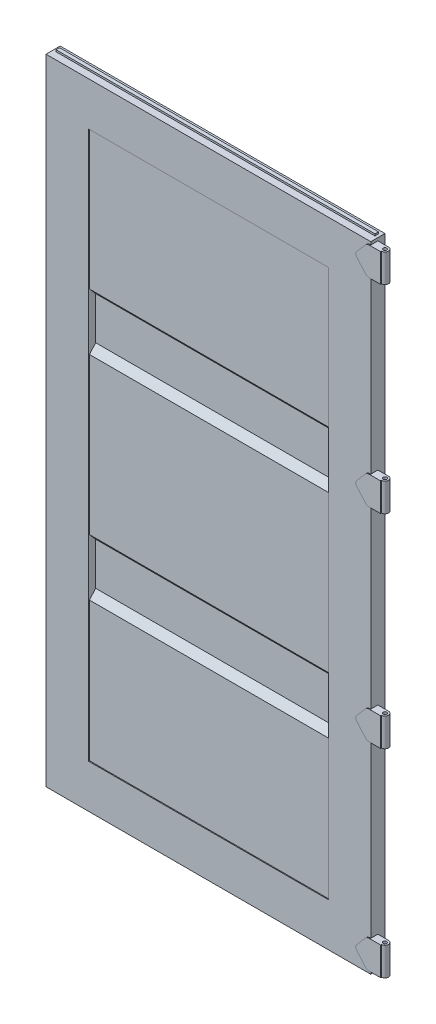
SolidWorks part; units mm, degrees
material "AISI 304"
ref_plane "Front Plane" through (0, 0, 0) normal (0, 0, 1) x (1, 0, 0)
ref_plane "Top Plane" through (0, 0, 0) normal (0, 1, 0) x (1, 0, 0)
ref_plane "Right Plane" through (0, 0, 0) normal (1, 0, 0) x (0, 0, -1)
sketch "Sketch2" plane through (0, 0, 0) normal (0, 1, 0) x (1, 0, 0)
  line L1 (-581.8187, 25.4) -> (-429.4187, 25.4)
  line L2 (-581.8187, 25.4) -> (-581.8187, -25.4)
  line L3 (-581.8187, -25.4) -> (-429.4187, -25.4)
  line L4 (-429.4187, 25.4) -> (-429.4187, -25.4)
  line L5 (-581.8187, 25.4) -> (-429.4187, -25.4) construction
  line L6 (-581.8187, -25.4) -> (-429.4187, 25.4) construction
  line L7 (581.8187, 25.4) -> (429.4187, 25.4)
  line L8 (581.8187, 25.4) -> (581.8187, -25.4)
  line L9 (581.8187, -25.4) -> (429.4187, -25.4)
  line L10 (429.4187, 25.4) -> (429.4187, -25.4)
  line L11 (581.8187, 25.4) -> (429.4187, -25.4) construction
  line L12 (581.8187, -25.4) -> (429.4187, 25.4) construction
  line L16 (578.6437, 22.225) -> (578.6437, -22.225)
  line L17 (578.6437, -22.225) -> (432.5937, -22.225)
  line L18 (432.5937, 22.225) -> (432.5937, -22.225)
  line L19 (578.6437, 22.225) -> (432.5937, 22.225)
  line L20 (-578.6437, 22.225) -> (-578.6437, -22.225)
  line L21 (-578.6437, -22.225) -> (-432.5937, -22.225)
  line L22 (-432.5937, 22.225) -> (-432.5937, -22.225)
  line L23 (-578.6437, 22.225) -> (-432.5937, 22.225)
  point P0 (-505.6187, 0)
  point P5 (505.6187, 0)
  point P10 (0, 0)
  point P11 (0, 0)
  point P12 (0, 0)
  point P13 (0, 0)
  dimension "D1" = 1163.6375
  dimension "D2" = 50.8
  dimension "D3" = 152.4
  dimension "D4" = 152.4
  dimension "D5" = 581.8187
  dimension "D6" = 3.175
  dimension "D7" = 3.175
extrude "Boss-Extrude1" add sketch "Sketch2" along normal mid plane 2266.95
sketch "Sketch3" plane through (429.4187, 0, 0) normal (-1, 0, 0) x (0, 0, 1)
  line L0 (19.05, 987.425) -> (0, 987.425)
  line L1 (0, 987.425) -> (0, 981.075)
  line L2 (0, 981.075) -> (25.4, 981.075)
  line L3 (25.4, 1133.475) -> (25.4, -1133.475) construction
  line L4 (25.4, 981.075) -> (25.4, 1133.475)
  line L5 (25.4, 1133.475) -> (-25.4, 1133.475)
  line L6 (-25.4, 1133.475) -> (-25.4, 1127.125)
  line L7 (-25.4, 1133.475) -> (-25.4, -1133.475) construction
  line L8 (-25.4, 1127.125) -> (19.05, 1127.125)
  line L9 (19.05, 1127.125) -> (19.05, 987.425)
  line L10 (-25.4, -1133.475) -> (25.4, -1133.475)
  line L11 (25.4, -1133.475) -> (25.4, -981.075)
  line L12 (25.4, -981.075) -> (0, -981.075)
  line L13 (0, -981.075) -> (0, -987.425)
  line L14 (0, -987.425) -> (19.05, -987.425)
  line L15 (19.05, -987.425) -> (19.05, -1127.125)
  line L16 (19.05, -1127.125) -> (-25.4, -1127.125)
  line L17 (-25.4, -1127.125) -> (-25.4, -1133.475)
  dimension "D1" = 6.35
  dimension "D2" = 6.35
  dimension "D3" = 6.35
  dimension "D4" = 152.4
  dimension "D5" = 25.4
  dimension "D6" = 6.35
  dimension "D7" = 6.35
  dimension "D8" = 6.35
  dimension "D9" = 25.4
  dimension "D10" = 152.4
extrude "Boss-Extrude4" add sketch "Sketch3" along normal up to surface (858.8375 mm away) up to face at (-429.4187, 0, 0)
sketch "Sketch5" plane through (-581.8187, 0, 0) normal (-1, 0, 0) x (0, 0, 1)
  line L0 (-25.4, -1133.475) -> (25.4, -1133.475) construction
  line L1 (-25.4, -1130.3) -> (25.4, -1130.3)
  line L2 (-25.4, -1130.3) -> (-25.4, -1136.65)
  line L3 (-25.4, -1136.65) -> (25.4, -1136.65)
  line L4 (25.4, -1130.3) -> (25.4, -1136.65)
  line L5 (-25.4, -1130.3) -> (25.4, -1136.65) construction
  line L6 (-25.4, -1136.65) -> (25.4, -1130.3) construction
  line L7 (-25.4, 1136.65) -> (25.4, 1136.65)
  line L8 (-25.4, 1136.65) -> (-25.4, 1130.3)
  line L9 (-25.4, 1130.3) -> (25.4, 1130.3)
  line L10 (25.4, 1136.65) -> (25.4, 1130.3)
  line L11 (-25.4, 1136.65) -> (25.4, 1130.3) construction
  line L12 (-25.4, 1130.3) -> (25.4, 1136.65) construction
  line L13 (25.4, 1133.475) -> (25.4, -1133.475) construction
  line L14 (-25.4, 1133.475) -> (25.4, 1133.475) construction
  point P0 (0, -1133.475)
  point P5 (0, 1133.475)
  point P12 (0, -1133.475)
  point P17 (0, 1133.475)
  dimension "D1" = 6.35
  dimension "D2" = 6.35
extrude "Boss-Extrude5" add sketch "Sketch5" against normal up to surface (1163.6375 mm away) up to face at (581.8187, 0, 0)
sketch "Sketch6" plane through (-429.4187, 0, 0) normal (1, 0, 0) x (0, 0, -1)
  line L0 (-15.875, -981.075) -> (-15.875, -482.6)
  line L1 (-25.4, -981.075) -> (0, -981.075) construction
  line L2 (-15.875, -482.6) -> (6.35, -457.2)
  line L3 (6.35, -457.2) -> (6.35, -304.8)
  line L4 (6.35, -304.8) -> (-15.875, -279.4)
  line L5 (-15.875, -279.4) -> (-15.875, 279.4)
  line L6 (-15.875, 279.4) -> (6.35, 304.8)
  line L7 (6.35, 304.8) -> (6.35, 457.2)
  line L8 (6.35, 457.2) -> (-15.875, 482.6)
  line L9 (-15.875, 482.6) -> (-15.875, 981.075)
  line L10 (0, 981.075) -> (-25.4, 981.075) construction
  line L11 (-15.875, 981.075) -> (-22.225, 981.075)
  line L12 (-22.225, 981.075) -> (-22.225, 482.6)
  line L13 (-22.225, 482.6) -> (0, 457.2)
  line L14 (0, 457.2) -> (0, 304.8)
  line L15 (0, 304.8) -> (-22.225, 279.4)
  line L16 (-22.225, 279.4) -> (-22.225, -279.4)
  line L17 (-22.225, -279.4) -> (0, -304.8)
  line L18 (0, -304.8) -> (0, -457.2)
  line L19 (0, -457.2) -> (-22.225, -482.6)
  line L20 (-22.225, -482.6) -> (-22.225, -981.075)
  line L21 (-22.225, -981.075) -> (-15.875, -981.075)
  line L22 (-25.4, 981.075) -> (-25.4, -981.075) construction
  point P14 (0, 0)
  point P28 (0, 0)
  point P29 (0, 0)
  point P30 (0, 0)
  point P31 (0, 0)
  point P32 (0, 247.428)
  point P33 (0, 399.828)
  point P34 (0, 0)
  point P35 (0, 0)
  point P36 (0, 0)
  point P37 (6.35, -492.0279)
  point P38 (0, 0)
  point P39 (6.35, -341.7856)
  point P40 (6.35, 191.7726)
  point P41 (-15.875, 0)
  point P42 (0, -381)
  point P43 (0, 381)
  dimension "D1" = 6.35
  dimension "D2" = 3.175
  dimension "D3" = 152.4
  dimension "D4" = 25.4
  dimension "D5" = 25.4
  dimension "D6" = 152.4
  dimension "D7" = 25.4
  dimension "D8" = 25.4
  dimension "D9" = 762
extrude "Boss-Extrude6" add sketch "Sketch6" along normal up to surface (858.8375 mm away) up to face at (429.4187, 0, 6.35)
sketch "Sketch1" plane through (0, 0, 0) normal (0, 0, 1) x (1, 0, 0)
  line L1 (-571.5, 1143) -> (571.5, 1143)
  line L2 (-571.5, 1143) -> (-571.5, -1143)
  line L3 (-571.5, -1143) -> (571.5, -1143)
  line L4 (571.5, 1143) -> (571.5, -1143)
  line L5 (-571.5, 1143) -> (571.5, -1143) construction
  line L6 (-571.5, -1143) -> (571.5, 1143) construction
  line L7 (571.5, 1123.95) -> (-571.5, 1123.95)
  line L8 (571.5, 1123.95) -> (571.5, -1123.95)
  line L9 (571.5, -1123.95) -> (-571.5, -1123.95)
  line L10 (-571.5, 1123.95) -> (-571.5, -1123.95)
  line L11 (571.5, 1123.95) -> (-571.5, -1123.95) construction
  line L12 (571.5, -1123.95) -> (-571.5, 1123.95) construction
  point P0 (0, 0)
  point P6 (0, 0)
  dimension "D1" = 1143
  dimension "D2" = 2286
  dimension "D3" = 19.05
sketch "Sketch7" plane through (0, 0, 25.4) normal (0, 0, 1) x (1, 0, 0)
  line L0 (571.5, 1143) -> (571.5, -1143) construction
  line L1 (533.4, 1126.49) -> (635, 1126.49)
  line L2 (533.4, 1126.49) -> (533.4, 1024.89)
  line L3 (533.4, 1024.89) -> (635, 1024.89)
  line L4 (635, 1126.49) -> (635, 1024.89)
  line L5 (533.4, 1126.49) -> (635, 1024.89) construction
  line L6 (533.4, 1024.89) -> (635, 1126.49) construction
  line L7 (533.4, 415.29) -> (635, 415.29)
  line L8 (533.4, 415.29) -> (533.4, 313.69)
  line L9 (533.4, 313.69) -> (635, 313.69)
  line L10 (635, 415.29) -> (635, 313.69)
  line L11 (533.4, 415.29) -> (635, 313.69) construction
  line L12 (533.4, 313.69) -> (635, 415.29) construction
  line L13 (533.4, -313.69) -> (635, -313.69)
  line L14 (533.4, -313.69) -> (533.4, -415.29)
  line L15 (533.4, -415.29) -> (635, -415.29)
  line L16 (635, -313.69) -> (635, -415.29)
  line L17 (533.4, -313.69) -> (635, -415.29) construction
  line L18 (533.4, -415.29) -> (635, -313.69) construction
  line L19 (533.4, -1024.89) -> (635, -1024.89)
  line L20 (533.4, -1024.89) -> (533.4, -1126.49)
  line L21 (533.4, -1126.49) -> (635, -1126.49)
  line L22 (635, -1024.89) -> (635, -1126.49)
  line L23 (533.4, -1024.89) -> (635, -1126.49) construction
  line L24 (533.4, -1126.49) -> (635, -1024.89) construction
  line L26 (581.8187, -1136.65) -> (-581.8187, -1136.65) construction
  line L27 (581.8187, 1136.65) -> (-581.8187, 1136.65) construction
  point P0 (584.2, 1075.69)
  point P7 (584.2, 364.49)
  point P12 (584.2, -364.49)
  point P17 (584.2, -1075.69)
  point P22 (577.85, 236.3168)
  dimension "D1" = 63.5
  dimension "D2" = 38.1
  dimension "D3" = 101.6
  dimension "D4" = 101.6
  dimension "D5" = 101.6
  dimension "D6" = 101.6
  dimension "D8" = 38.1
  dimension "D10" = 38.1
  dimension "D12" = 38.1
  dimension "D13" = 711.2
  dimension "D14" = 711.2
  dimension "D15" = 10.16
  dimension "D16" = 10.16
extrude "Boss-Extrude7" add sketch "Sketch7" against normal blind 25.4
extrude "Boss-Extrude8" add sketch "Sketch1" against normal blind 12.7 contours L4 L9 L2 L3 | L7 L4 L1 L2
sketch "Sketch9" plane through (0, 0, 25.4) normal (0, 0, 1) x (1, 0, 0)
  line L0 (581.8187, 1024.89) -> (581.8187, 415.29) construction
  line L1 (635, 1126.49) -> (635, 1024.89)
  line L2 (635, 1024.89) -> (579.5385, 1024.89)
  line L3 (566.19, 1030.925) -> (534.1841, 1067.3007)
  line L4 (635, 1126.49) -> (579.5385, 1126.49)
  line L5 (566.19, 1120.455) -> (534.1841, 1084.0793)
  line L6 (635, 415.29) -> (635, 313.69)
  line L7 (635, 313.69) -> (578.9049, 313.69)
  line L8 (565.4406, 319.8579) -> (534.1014, 356.1956)
  line L9 (635, 415.29) -> (578.9049, 415.29)
  line L10 (565.4406, 409.1221) -> (534.1014, 372.7844)
  line L11 (635, 313.69) -> (635, 415.29) construction
  line L12 (581.8187, 313.69) -> (581.8187, -313.69) construction
  line L13 (581.8187, 313.69) -> (635, 313.69) construction
  line L19 (635, -415.29) -> (635, -313.69) construction
  line L20 (635, -313.69) -> (581.8187, -313.69) construction
  line L21 (581.8187, -415.29) -> (581.8187, -1024.89) construction
  line L22 (635, -313.69) -> (635, -415.29)
  line L23 (635, -415.29) -> (578.9049, -415.29)
  line L24 (565.4406, -409.1221) -> (534.1014, -372.7844)
  line L25 (635, -313.69) -> (578.9049, -313.69)
  line L26 (565.4406, -319.8579) -> (534.1014, -356.1956)
  line L27 (635, -1024.89) -> (635, -1126.49)
  line L28 (635, -1126.49) -> (578.9049, -1126.49)
  line L29 (565.4406, -1120.3221) -> (534.1014, -1083.9844)
  line L30 (635, -1024.89) -> (578.9049, -1024.89)
  line L31 (565.4406, -1031.0579) -> (534.1014, -1067.3956)
  line L32 (635, -1126.49) -> (635, -1024.89) construction
  line L33 (635, -1024.89) -> (581.8187, -1024.89) construction
  arc A0 (534.1841, 1084.0793) -> (534.1841, 1067.3007) centre (543.7187, 1075.69) ccw
  arc A1 (579.5385, 1024.89) -> (566.19, 1030.925) centre (579.5385, 1042.67) cw
  arc A2 (566.19, 1120.455) -> (579.5385, 1126.49) centre (579.5385, 1108.71) cw
  arc A3 (534.1014, 372.7844) -> (534.1014, 356.1956) centre (543.7187, 364.49) ccw
  arc A4 (578.9049, 313.69) -> (565.4406, 319.8579) centre (578.9049, 331.47) cw
  arc A5 (565.4406, 409.1221) -> (578.9049, 415.29) centre (578.9049, 397.51) cw
  arc A9 (534.1014, -356.1956) -> (534.1014, -372.7844) centre (543.7187, -364.49) ccw
  arc A10 (578.9049, -415.29) -> (565.4406, -409.1221) centre (578.9049, -397.51) cw
  arc A11 (565.4406, -319.8579) -> (578.9049, -313.69) centre (578.9049, -331.47) cw
  arc A12 (534.1014, -1067.3956) -> (534.1014, -1083.9844) centre (543.7187, -1075.69) ccw
  arc A13 (578.9049, -1126.49) -> (565.4406, -1120.3221) centre (578.9049, -1108.71) cw
  arc A14 (565.4406, -1031.0579) -> (578.9049, -1024.89) centre (578.9049, -1042.67) cw
  point P1 (0, 0)
  point P11 (0, 0)
  point P13 (0, 0)
  point P14 (0, 0)
  point P15 (635, 1075.69)
  point P16 (533.4, 1075.69)
  point P19 (571.5, 1024.89)
  point P22 (571.5, 1126.49)
  point P30 (635, 364.49)
  point P37 (635, 364.49)
  point P38 (518.9569, 356.4472)
  point P39 (0, 0)
  point P42 (0, 0)
  point P43 (543.7772, 317.0896)
  point P46 (563.19, 397.51)
  point P47 (571.5, 413.6747)
  point P55 (635, -364.49)
  point P62 (635, -364.49)
  point P63 (571.5, -315.3053)
  point P68 (562.3632, -397.51)
  point P76 (635, -1075.69)
  point P81 (571.5, -1026.5053)
  point P84 (635, -1075.69)
  point P87 (0, 0)
  dimension "D1" = 38.1
  dimension "D2" = 63.5
  dimension "D3" = 12.7
  dimension "D4" = 17.78
  dimension "D5" = 12.7
  dimension "D6" = 17.78
  dimension "D9" = 12.7
  dimension "D10" = 17.78
  dimension "D13" = 12.7
  dimension "D14" = 17.78
  dimension "D7" = 38.1
  dimension "D8" = 63.5
  dimension "D11" = 63.5
  dimension "D12" = 38.1
  dimension "D15" = 63.5
  dimension "D16" = 38.1
extrude "Boss-Extrude9" add sketch "Sketch9" along normal blind 3.175
sketch "Sketch8" plane through (0, 1126.49, 0) normal (0, 1, 0) x (1, 0, 0)
  line L0 (581.8187, -25.4) -> (581.8187, 0) construction
  line L1 (635, 0) -> (581.8187, 0) construction
  line L2 (619.9187, 0) -> (635, 0)
  line L3 (635, 0) -> (635, -28.575)
  line L4 (635, -28.575) -> (619.9187, -28.575)
  line L5 (635, -28.575) -> (579.5385, -28.575) construction
  line L6 (619.9187, -28.575) -> (619.9187, -25.4)
  circle A0 centre (619.9187, -12.7) radius 6.35
  arc A1 (619.9187, -25.4) -> (619.9187, 0) centre (619.9187, -12.7) ccw
  point P6 (609.6, 0)
  line M4 (635, 0) -> (581.8187, 0)
  dimension "D1" = 12.7
  dimension "D2" = 38.1
  dimension "D3" = 12.7
extrude "Cut-Extrude1" cut sketch "Sketch8" against normal up to surface (2252.98 mm away) contours A1 L3 M4 | A0
